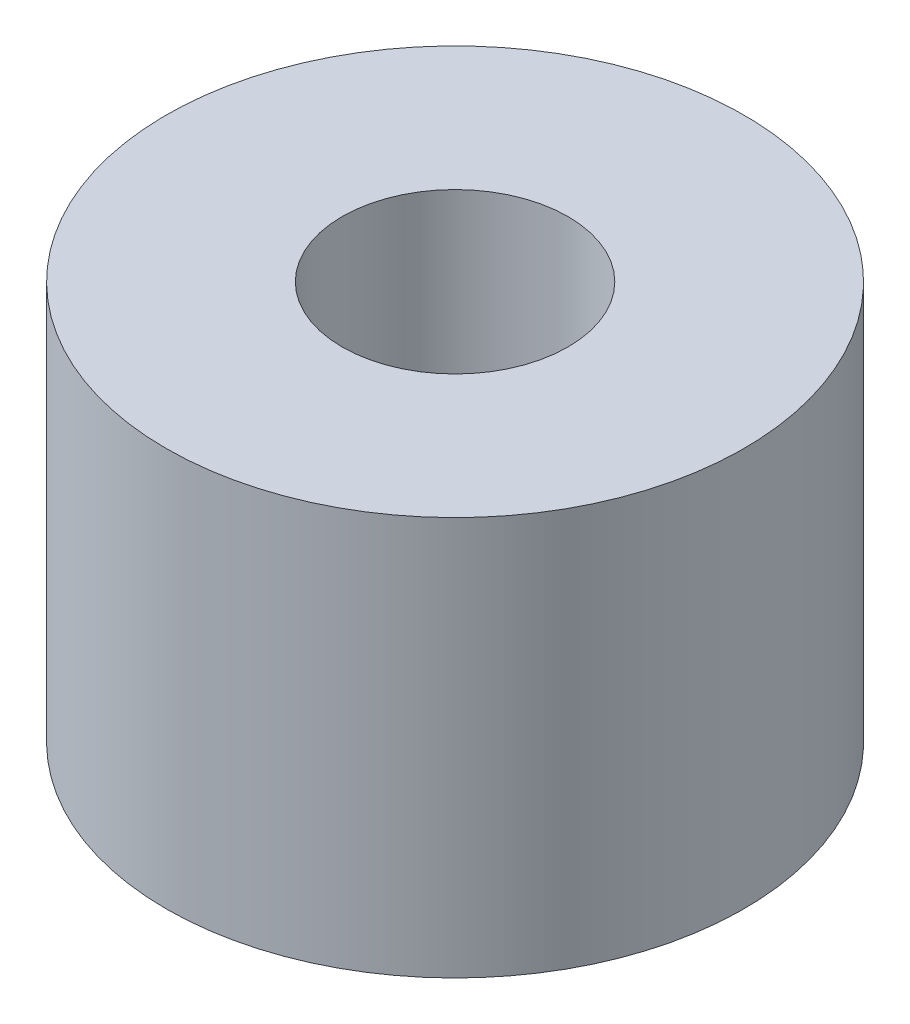
SolidWorks part; units mm, degrees
material "6061-T6 (SS)"
ref_plane "Front Plane" through (0, 0, 0) normal (0, 0, 1) x (1, 0, 0)
ref_plane "Top Plane" through (0, 0, 0) normal (0, 1, 0) x (1, 0, 0)
ref_plane "Right Plane" through (0, 0, 0) normal (1, 0, 0) x (0, 0, -1)
sketch "Sketch1" plane through (0, 0, 0) normal (0, 1, 0) x (1, 0, 0)
  circle A0 centre (0, 0) radius 8.2804
  circle A1 centre (0, 0) radius 3.2385
  dimension "D1" = 6.477
  dimension "D2" = 16.5608
extrude "Boss-Extrude1" add sketch "Sketch1" along normal blind 11.43
